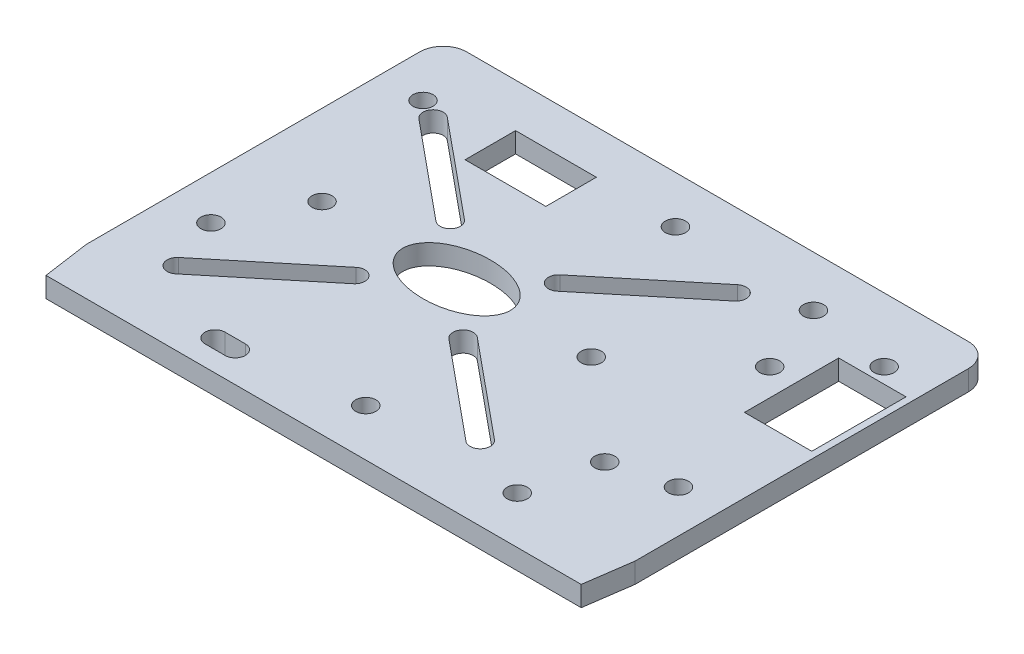
SolidWorks part; units mm, degrees
ref_plane "Alzado" through (0, 0, 0) normal (0, 0, 1) x (1, 0, 0)
ref_plane "Planta" through (0, 0, 0) normal (0, 1, 0) x (1, 0, 0)
ref_plane "Vista lateral" through (0, 0, 0) normal (1, 0, 0) x (0, 0, -1)
sketch "Croquis1" plane through (0, 0, 0) normal (0, 1, 0) x (1, 0, 0)
  line L0 (34.25, 18.5) -> (38.1708, 18.5) construction
  line L2 (40.75, -26.5) -> (40.75, 23)
  line L3 (37.25, 26.5) -> (-37.25, 26.5)
  line L4 (-40.75, -26.5) -> (-40.75, 23)
  line L5 (40.75, -26.5) -> (-40.75, 26.5) construction
  line L6 (40.75, 26.5) -> (-40.75, -26.5) construction
  line L7 (35.75, 17) -> (35.75, 14.7708) construction
  line L8 (0, 0) -> (0, 15.2558) construction
  line L9 (34.25, 15.5) -> (43.2827, 15.5) construction
  line L10 (29.75, 14.75) -> (39.75, 14.75)
  line L11 (29.75, 14.75) -> (29.75, 0.75)
  line L12 (29.75, 0.75) -> (39.75, 0.75)
  line L13 (39.75, 14.75) -> (39.75, 0.75)
  line L14 (-39.75, -33.5) -> (39.75, -33.5)
  line L15 (-40.75, -26.5) -> (-39.75, -33.5)
  line L16 (39.75, -33.5) -> (40.75, -26.5)
  line L17 (35.95, -13.75) -> (35.95, -21.167) construction
  line L18 (34.45, -12.25) -> (43.6736, -12.25) construction
  line L19 (27.25, -16) -> (27.25, -24.1423) construction
  line L20 (25.75, -17.5) -> (29.4582, -17.5) construction
  line L21 (14.75, 26.5) -> (14.75, -33.5) construction
  line L22 (25.75, 7) -> (17.8119, 7) construction
  line L23 (25.75, -14.5) -> (20.715, -14.5) construction
  line L24 (23.25, 19) -> (23.25, 16.2641) construction
  line L25 (21.75, 20.5) -> (20.3356, 20.5) construction
  line L26 (-8.75, -3.5) -> (4.2834, 19.0745) construction
  line L27 (-8.75, -3.5) -> (20.7197, -3.5) construction
  line L28 (-8.75, -3.5) -> (5.1122, -26.5) construction
  line L29 (-0.704, 3.5874) -> (13.75, 15.5) construction
  line L30 (-1.658, 4.7449) -> (12.796, 16.6575)
  line L31 (0.25, 2.4298) -> (14.704, 14.3425)
  line L32 (15.25, 15.5) -> (15.25, -1.4107) construction
  line L33 (-8.75, -3.5) -> (-8.75, 34.8713) construction
  line L34 (9.085, 17) -> (13.75, 17) construction
  line L35 (-0.704, -10.5874) -> (13.75, -22.5) construction
  line L36 (-1.658, -11.7449) -> (12.796, -23.6575)
  line L37 (0.25, -9.4298) -> (14.704, -21.3425)
  line L38 (-16.796, -10.5874) -> (-31.25, -22.5) construction
  line L39 (-15.842, -11.7449) -> (-30.296, -23.6575)
  line L40 (-17.75, -9.4298) -> (-32.204, -21.3425)
  line L41 (-16.796, 3.5874) -> (-31.25, 15.5) construction
  line L42 (-15.842, 4.7449) -> (-30.296, 16.6575)
  line L43 (-17.75, 2.4298) -> (-32.204, 14.3425)
  line L44 (2.25, -26.5) -> (2.25, -28.6171) construction
  line L45 (21.75, -26.5) -> (21.75, -29) construction
  line L46 (-35.75, -14.5) -> (-35.75, -13.75) construction
  line L47 (-34.25, -16) -> (-32.75, -16) construction
  line L48 (-19.1429, -29) -> (-16.1429, -29) construction
  line L49 (-19.1429, -27.5) -> (-16.1429, -27.5)
  line L50 (-19.1429, -30.5) -> (-16.1429, -30.5)
  line L51 (-20.6429, -29) -> (-20.6429, -30.9263) construction
  line L52 (-19.1429, -29) -> (-40.3929, -29) construction
  line L54 (-23.5, 20) -> (-11.5, 20)
  line L55 (-23.5, 20) -> (-23.5, 12.5)
  line L56 (-23.5, 12.5) -> (-11.5, 12.5)
  line L57 (-11.5, 20) -> (-11.5, 12.5)
  arc A0 (40.75, 23) -> (37.25, 26.5) centre (37.25, 23) ccw
  arc A1 (-37.25, 26.5) -> (-40.75, 23) centre (-37.25, 23) ccw
  circle A2 centre (34.25, 17) radius 1.5
  circle A3 centre (-34.25, 17) radius 1.5
  circle A4 centre (34.45, -13.75) radius 1.5
  circle A5 centre (25.75, -16) radius 1.5
  circle A6 centre (23.25, -26.5) radius 1.5
  circle A7 centre (25.75, 8.5) radius 1.5
  circle A8 centre (21.75, 19) radius 1.5
  arc A9 (-1.658, 4.7449) -> (0.25, 2.4298) centre (-0.704, 3.5874) ccw
  arc A10 (14.704, 14.3425) -> (12.796, 16.6575) centre (13.75, 15.5) ccw
  arc A11 (-1.658, -11.7449) -> (0.25, -9.4298) centre (-0.704, -10.5874) cw
  arc A12 (14.704, -21.3425) -> (12.796, -23.6575) centre (13.75, -22.5) cw
  arc A13 (-15.842, -11.7449) -> (-17.75, -9.4298) centre (-16.796, -10.5874) ccw
  arc A14 (-32.204, -21.3425) -> (-30.296, -23.6575) centre (-31.25, -22.5) ccw
  arc A15 (-15.842, 4.7449) -> (-17.75, 2.4298) centre (-16.796, 3.5874) cw
  arc A16 (-32.204, 14.3425) -> (-30.296, 16.6575) centre (-31.25, 15.5) cw
  circle A17 centre (11.25, -3.5) radius 1.5
  circle A18 centre (-28.75, -3.5) radius 1.5
  circle A19 centre (0.75, -26.5) radius 1.5
  circle A20 centre (0.75, 19.5) radius 1.5
  circle A21 centre (-34.25, -14.5) radius 1.5
  arc A22 (-19.1429, -27.5) -> (-19.1429, -30.5) centre (-19.1429, -29) ccw
  arc A23 (-16.1429, -30.5) -> (-16.1429, -27.5) centre (-16.1429, -29) ccw
  ellipse E0 centre (-8.75, -3.5) end of major axis (-0.75, -3.5) minor radius 5
  point P0 (0, 0)
  point P70 (6.523, 9.5437)
  point P83 (6.523, -16.5437)
  point P90 (-24.023, -16.5437)
  point P97 (-24.023, 9.5437)
  point P122 (-17.6429, -29)
  dimension "D3" = 3.5
  dimension "D4" = 3
  dimension "D14" = 3
  dimension "D17" = 3
  dimension "D20" = 3
  dimension "D23" = 3
  dimension "D25" = 3
  dimension "D40" = 3
  dimension "D41" = 3
  dimension "D43" = 3
  dimension "D1" = 81.5
  dimension "D2" = 1
  dimension "D5" = 8
  dimension "D6" = 5
  dimension "D7" = 14
  dimension "D8" = 10
  dimension "D9" = 0.75
  dimension "D10" = 1
  dimension "D11" = 79.5
  dimension "D12" = 60
  dimension "D13" = 26.5
  dimension "D15" = 4.8
  dimension "D16" = 13
  dimension "D18" = 13.5
  dimension "D19" = 16
  dimension "D21" = 17.5
  dimension "D22" = 26
  dimension "D24" = 21.5
  dimension "D26" = 6
  dimension "D27" = 17.5
  dimension "D28" = 25
  dimension "D29" = 25
  dimension "D30" = 24
  dimension "D31" = 16
  dimension "D32" = 60
  dimension "D33" = 58.923
  dimension "D34" = 9
  dimension "D35" = 24
  dimension "D36" = 3
  dimension "D37" = 9.5
  dimension "D38" = 21.7551
  dimension "D39" = 12
  dimension "D42" = 19.5
  dimension "D44" = 5
  dimension "D45" = 17.5
  dimension "D46" = 3
  dimension "D47" = 3
  dimension "D48" = 19.75
  dimension "D49" = 3
  dimension "D50" = 7.5
  dimension "D51" = 12
  dimension "D52" = 52.25
  dimension "D53" = 6.5
extrude "Saliente-Extruir1" add sketch "Croquis1" along normal blind 3
